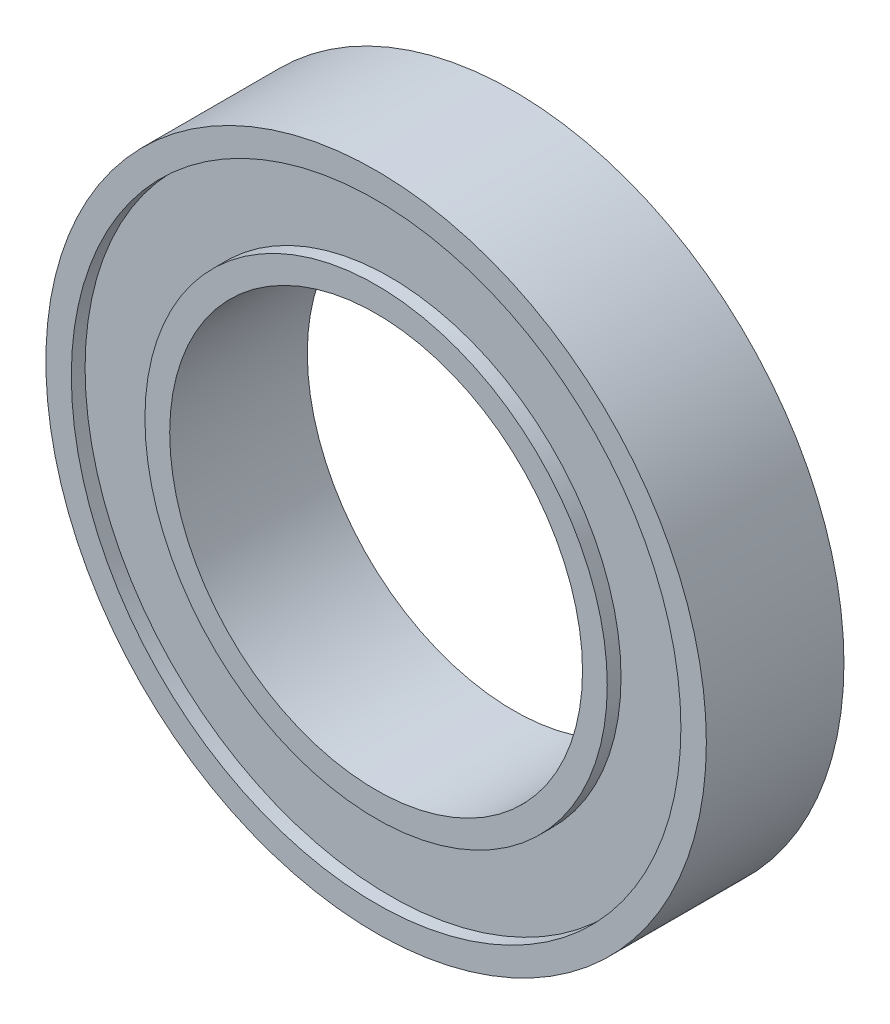
SolidWorks part; units mm, degrees
material "鉻不鏽鋼"
ref_plane "前基準面" through (0, 0, 0) normal (0, 0, 1) x (1, 0, 0)
ref_plane "上基準面" through (0, 0, 0) normal (0, 1, 0) x (1, 0, 0)
ref_plane "右基準面" through (0, 0, 0) normal (1, 0, 0) x (0, 0, -1)
sketch "草圖1" plane through (0, 0, 0) normal (0, 0, 1) x (1, 0, 0)
  circle A0 centre (0, 0) radius 12
  dimension "D1" = 24
extrude "填料-伸長1" add sketch "草圖1" along normal blind 5
sketch "草圖2" plane through (0, 0, 5) normal (0, 0, 1) x (1, 0, 0)
  circle A0 centre (0, 0) radius 7.5
  dimension "D1" = 15
extrude "除料-伸長1" cut sketch "草圖2" against normal through all
sketch "草圖3" plane through (0, 0, 5) normal (0, 0, 1) x (1, 0, 0)
  circle A0 centre (0, 0) radius 8.4
  circle A1 centre (0, 0) radius 11.075
  dimension "D1" = 22.15
  dimension "D2" = 16.8
extrude "除料-伸長2" cut sketch "草圖3" against normal blind 0.5
sketch "草圖4" plane through (0, 0, 0) normal (0, 0, -1) x (-1, 0, 0)
  circle A0 centre (0, 0) radius 8.4
  circle A1 centre (0, 0) radius 11.075
  dimension "D1" = 16.8
  dimension "D2" = 22.15
extrude "除料-伸長3" cut sketch "草圖4" against normal blind 0.5
